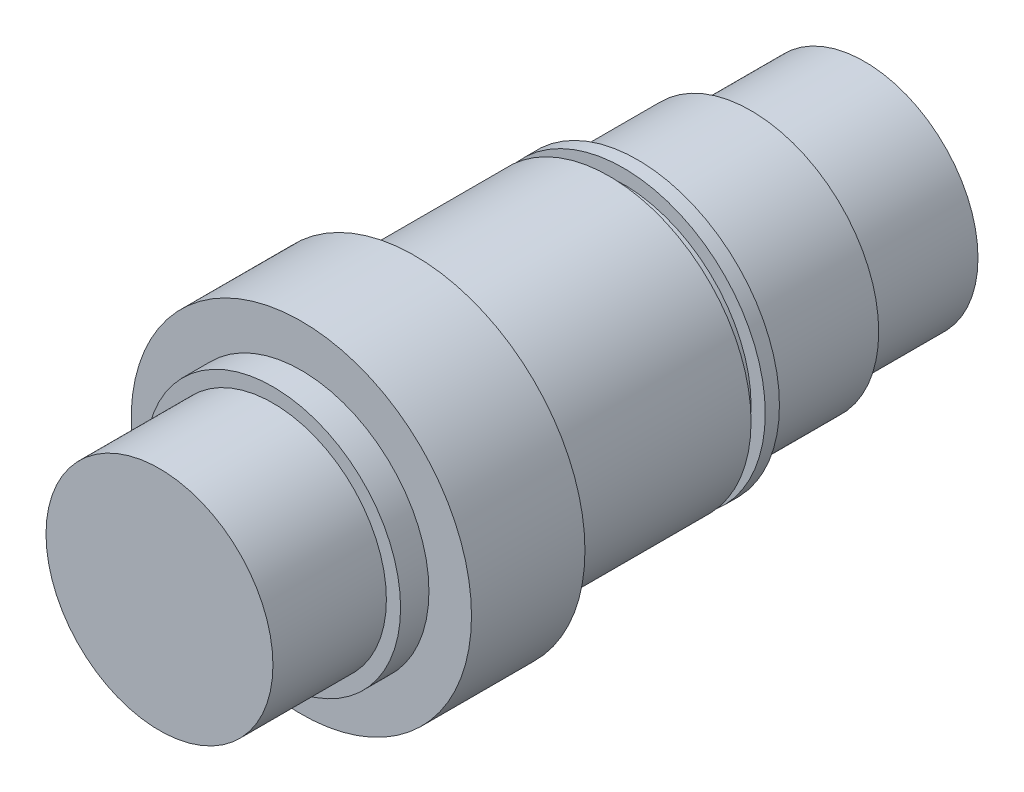
SolidWorks part; units mm, degrees
ref_plane "Front Plane" through (0, 0, 0) normal (0, 0, 1) x (1, 0, 0)
ref_plane "Top Plane" through (0, 0, 0) normal (0, 1, 0) x (1, 0, 0)
ref_plane "Right Plane" through (0, 0, 0) normal (1, 0, 0) x (0, 0, -1)
sketch "Sketch2" plane through (0, 0, 0) normal (0, 0, 1) x (1, 0, 0)
  circle A0 centre (0, 0) radius 25.4
  dimension "D1" = 50.8
extrude "Boss-Extrude1" add sketch "Sketch2" along normal blind 25.4
sketch "Sketch3" plane through (0, 0, 25.4) normal (0, 0, 1) x (1, 0, 0)
  circle A0 centre (0, 0) radius 28.575
  dimension "D1" = 57.15
extrude "Boss-Extrude2" add sketch "Sketch3" along normal blind 25.4
sketch "Sketch4" plane through (0, 0, 50.8) normal (0, 0, 1) x (1, 0, 0)
  circle A0 centre (0, 0) radius 31.75
  dimension "D1" = 63.5
extrude "Boss-Extrude3" add sketch "Sketch4" along normal blind 3.175
sketch "Sketch5" plane through (0, 0, 53.975) normal (0, 0, 1) x (1, 0, 0)
  circle A0 centre (0, 0) radius 28.575
  circle A1 centre (0, 0) radius 31.75 construction
  dimension "D1" = 3.175
extrude "Boss-Extrude4" add sketch "Sketch5" along normal blind 3.175
sketch "Sketch6" plane through (0, 0, 57.15) normal (0, 0, 1) x (1, 0, 0)
  circle A0 centre (0, 0) radius 31.75
  circle A1 centre (0, 0) radius 28.575 construction
  dimension "D1" = 3.175
extrude "Boss-Extrude5" add sketch "Sketch6" along normal blind 43.5356
sketch "Sketch7" plane through (0, 0, 100.6856) normal (0, 0, 1) x (1, 0, 0)
  circle A0 centre (0, 0) radius 38.1
  dimension "D1" = 76.2
extrude "Boss-Extrude6" add sketch "Sketch7" along normal blind 25.4
sketch "Sketch8" plane through (0, 0, 126.0856) normal (0, 0, 1) x (1, 0, 0)
  circle A0 centre (0, 0) radius 28.575
  dimension "D1" = 57.15
extrude "Boss-Extrude7" add sketch "Sketch8" along normal blind 6.35
sketch "Sketch9" plane through (0, 0, 132.4356) normal (0, 0, 1) x (1, 0, 0)
  circle A0 centre (0, 0) radius 25.4
  dimension "D1" = 50.8
extrude "Boss-Extrude8" add sketch "Sketch9" along normal blind 25.4
ref_plane "Plane4" through (0, -31.75, 0) normal (0, -1, 0) x (-1, 0, 0)
sketch "Sketch10" plane through (0, -31.75, 0) normal (0, -1, 0) x (-1, 0, 0)
  line L0 (0, -69.3928) -> (0, -88.4428) construction
  line L3 (3.175, -69.3928) -> (3.175, -88.4428)
  line L4 (-3.175, -69.3928) -> (-3.175, -88.4428)
  line L5 (-31.75, -57.15) -> (-31.75, -100.6856) construction
  arc A2 (3.175, -69.3928) -> (-3.175, -69.3928) centre (0, -69.3928) ccw
  arc A3 (-3.175, -88.4428) -> (3.175, -88.4428) centre (0, -88.4428) ccw
  point P3 (0, -78.9178)
  point P8 (0, -66.2178)
  point P9 (0, -91.6178)
  point P15 (-31.75, -78.9178)
  dimension "D2" = 3.175
  dimension "D1" = 25.4
extrude "Cut-Extrude1" cut sketch "Sketch10" against normal blind 3.175
